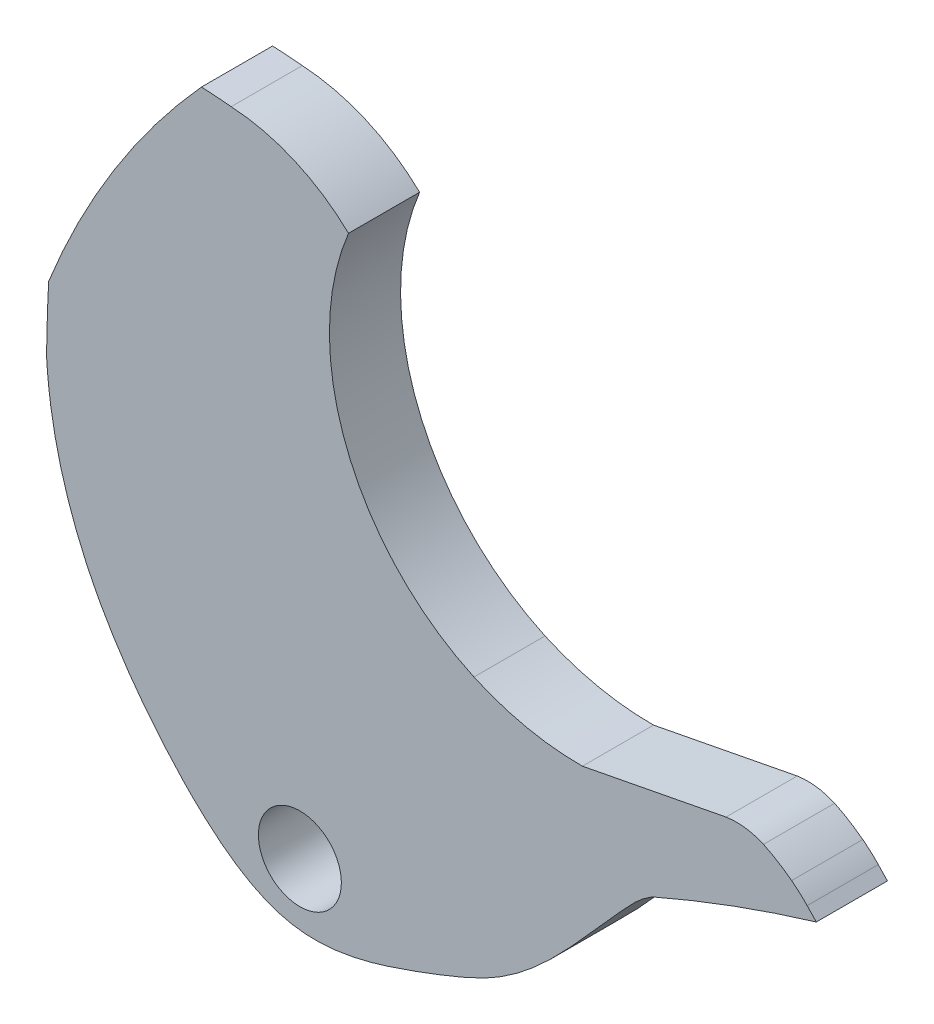
SolidWorks part; units mm, degrees
ref_plane "Front Plane" through (0, 0, 0) normal (0, 0, 1) x (1, 0, 0)
ref_plane "Top Plane" through (0, 0, 0) normal (0, 1, 0) x (1, 0, 0)
ref_plane "Right Plane" through (0, 0, 0) normal (1, 0, 0) x (0, 0, -1)
sketch "Sketch1" plane through (0, 0, 0) normal (0, 0, 1) x (1, 0, 0)
  line L6 (19.9304, 2.906) -> (13.8715, 1.7355)
  line L8 (19.8434, 3.3984) -> (13.8201, 2.2348) construction
  line L9 (23.3513, 1.3807) -> (23.7364, 0.9749)
  arc A1 (9.296, 2.7032) -> (13.8715, 1.7355) centre (13.8009, 12.7021) ccw
  arc A3 (-8.7275, 5.4133) -> (-8.6834, 4.7998) centre (10.2018, 6.4675) ccw
  circle A4 centre (1.9556, -7.6051) radius 1.75
  arc A5 (-2.1972, 18.5047) -> (-8.639, 8.1896) centre (23.1641, -4.5028) ccw
  arc A6 (-8.7275, 5.4133) -> (-8.639, 8.1896) centre (60.6416, 4.5919) cw
  arc A7 (-0.9419, 18.416) -> (-2.1972, 18.5047) centre (-2.993, -1.692) ccw
  arc A46 (23.7364, 0.9749) -> (16.8282, -1.5614) centre (41.4115, -57.8448) ccw
  arc A48 (4.0068, 16.2659) -> (-0.9419, 18.416) centre (-1.3941, 10.6053) ccw
  arc A49 (4.0068, 16.2659) -> (9.296, 2.7032) centre (13.7019, 12.2341) ccw
  arc A59 (21.5093, 2.6995) -> (19.9304, 2.906) centre (20.3708, 0.1345) ccw
  arc A60 (22.6965, 1.9686) -> (21.5093, 2.6995) centre (18.448, -3.6031) ccw
  arc A61 (23.3513, 1.3807) -> (22.6965, 1.9686) centre (19.3616, -2.405) ccw
  arc A63 (-0.8887, 18.9137) -> (-1.6646, 19.0237) centre (-5.6021, -11.5617) ccw construction
  arc A64 (4.6015, 16.3793) -> (-0.8887, 18.9137) centre (-1.3941, 10.6053) ccw construction
  arc A65 (9.5058, 3.157) -> (3.7142, 12.7286) centre (13.7019, 12.2341) ccw construction
  arc A66 (9.296, 2.7032) -> (3.2148, 12.7534) centre (13.7019, 12.2341) ccw construction
  arc A67 (4.6015, 16.3793) -> (9.5058, 3.157) centre (13.7019, 12.2341) ccw construction
  arc A68 (3.7142, 12.7286) -> (13.8201, 2.2348) centre (13.7019, 12.2341) ccw construction
  arc A69 (21.7201, 3.1529) -> (19.8434, 3.3984) centre (20.3708, 0.1345) ccw construction
  arc A70 (22.9997, 2.3662) -> (21.7201, 3.1529) centre (18.448, -3.6031) ccw construction
  arc A71 (24.2186, 1.1176) -> (22.9997, 2.3662) centre (19.3616, -2.405) ccw construction
  arc A72 (24.2186, 1.1176) -> (16.8282, -1.5614) centre (41.4115, -57.8448) ccw construction
  arc A73 (23.3513, 1.3807) -> (16.628, -1.1032) centre (41.4115, -57.8448) ccw construction
  arc A74 (-0.9419, 18.416) -> (-1.7284, 18.5278) centre (-5.6021, -11.5617) ccw construction
  arc A75 (3.2148, 12.7534) -> (13.8715, 1.7355) centre (13.7019, 12.2341) ccw construction
  spline S59 degree 3 poles (9.6203, -8.1278) (9.8004, -8.0368) (9.9773, -7.9418) (10.3229, -7.7426) (10.491, -7.6386) (10.9901, -7.3074) (11.3127, -7.0642) (12.2426, -6.2911) (12.8209, -5.712) (13.9463, -4.5015) (14.4923, -3.8697) (15.1849, -3.0958) (15.3236, -2.9423) (15.6021, -2.6377) (15.7438, -2.4834) (16.0298, -2.1861) (16.1694, -2.0475) (16.4793, -1.7858) (16.6529, -1.6645) (16.8282, -1.5614) knots 0 0 0 0 0.0625 0.0625 0.125 0.125 0.25 0.25 0.5 0.5 0.75 0.75 0.8125 0.8125 0.875 0.875 0.9375 0.9375 1 1 1 1
  spline S60 degree 3 poles (6.8115, -9.2847) (7.0565, -9.1959) (7.2978, -9.1063) (7.7768, -8.924) (8.0156, -8.8311) (8.7224, -8.5475) (9.1798, -8.3504) (9.6203, -8.1278) knots 0 0 0 0 0.25 0.25 0.5 0.5 1 1 1 1
  spline S61 degree 3 poles (4.2275, -10.0642) (5.0898, -9.8847) (5.9628, -9.5922) (6.8115, -9.2847) knots 0 0 0 0 1 1 1 1
  spline S62 degree 3 poles (1.6028, -10.1599) (2.0199, -10.2364) (2.459, -10.26) (3.3373, -10.2204) (3.7799, -10.1574) (4.2275, -10.0642) knots 0 0 0 0 0.5 0.5 1 1 1 1
  spline S63 degree 3 poles (-2.9738, -7.2038) (-2.3064, -7.903) (-1.5903, -8.5657) (-0.4454, -9.3523) (-0.0535, -9.5795) (0.557, -9.8537) (0.7641, -9.9339) (1.1818, -10.0677) (1.391, -10.121) (1.6028, -10.1599) knots 0 0 0 0 0.5 0.5 0.75 0.75 0.875 0.875 1 1 1 1
  spline S64 degree 3 poles (-7.064, -1.2813) (-6.5752, -2.3411) (-5.9851, -3.3612) (-4.9576, -4.8426) (-4.5919, -5.3291) (-3.818, -6.2818) (-3.4088, -6.7481) (-2.9738, -7.2038) knots 0 0 0 0 0.5 0.5 0.75 0.75 1 1 1 1
  spline S65 degree 3 poles (-8.6834, 4.7998) (-8.5881, 3.7212) (-8.4023, 2.6745) (-7.8594, 0.6485) (-7.5021, -0.3316) (-7.064, -1.2813) knots 0 0 0 0 0.5 0.5 1 1 1 1
  dimension "D1" = 0.5
extrude "Boss-Extrude1" add sketch "Sketch1" along normal blind 3
